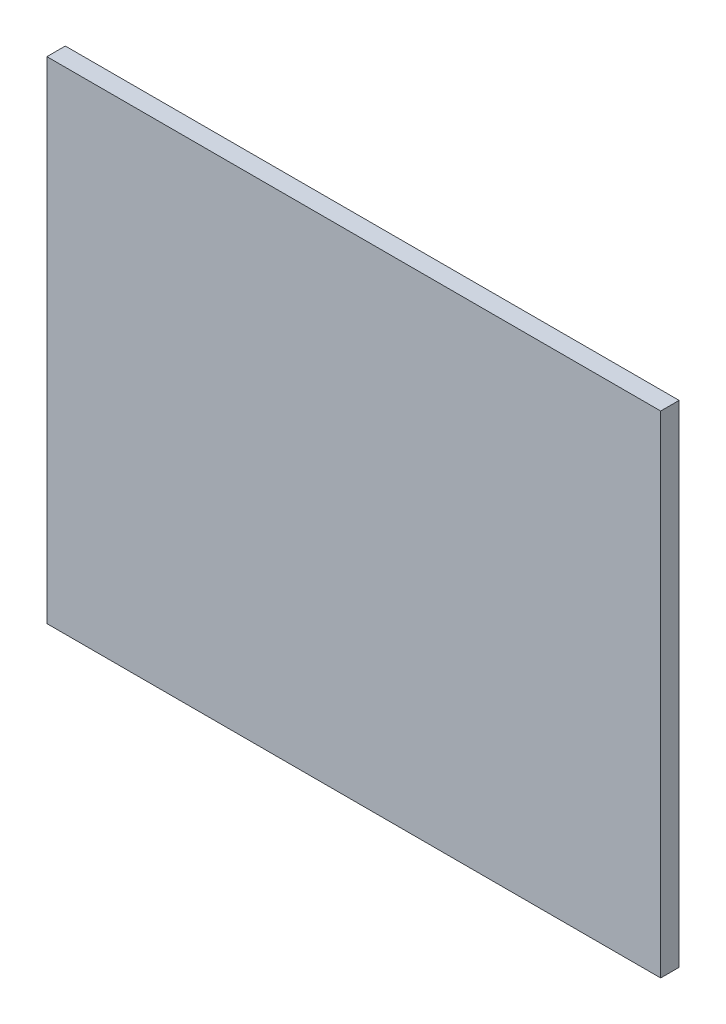
SolidWorks part; units mm, degrees
ref_plane "Přední rovina" through (0, 0, 0) normal (0, 0, 1) x (1, 0, 0)
ref_plane "Horní rovina" through (0, 0, 0) normal (0, 1, 0) x (1, 0, 0)
ref_plane "Pravá rovina" through (0, 0, 0) normal (1, 0, 0) x (0, 0, -1)
sketch "Skica1" plane through (0, 0, 0) normal (0, 0, 1) x (1, 0, 0)
  line L1 (0, 0) -> (100, 0)
  line L2 (0, 0) -> (0, 80)
  line L3 (0, 80) -> (100, 80)
  line L4 (100, 0) -> (100, 80)
  dimension "D1" = 100
  dimension "D2" = 80
extrude "Přidat vysunutím1" add sketch "Skica1" along normal blind 3
sketch "Skica2" plane through (0, 0, 3) normal (0, 0, 1) x (1, 0, 0)
  line L0 (100, 80) -> (0, 80) construction
  line L1 (0, 80) -> (0, 0) construction
  line L2 (100, 40) -> (0, 40) construction
  line L3 (100, 0) -> (100, 80) construction
  line L4 (50, 80) -> (50, 0) construction
  line L5 (0, 0) -> (100, 0) construction
  circle A0 centre (4, 76) radius 3
  circle A1 centre (96, 76) radius 3
  circle A2 centre (96, 4) radius 3
  circle A3 centre (4, 4) radius 3
  dimension "D1" = 6
  dimension "D2" = 1
  dimension "D3" = 1
extrude "Odebrat vysunutím1" cut sketch "Skica2" against normal blind 1.4 from offset 0.4 offset against normal yes
